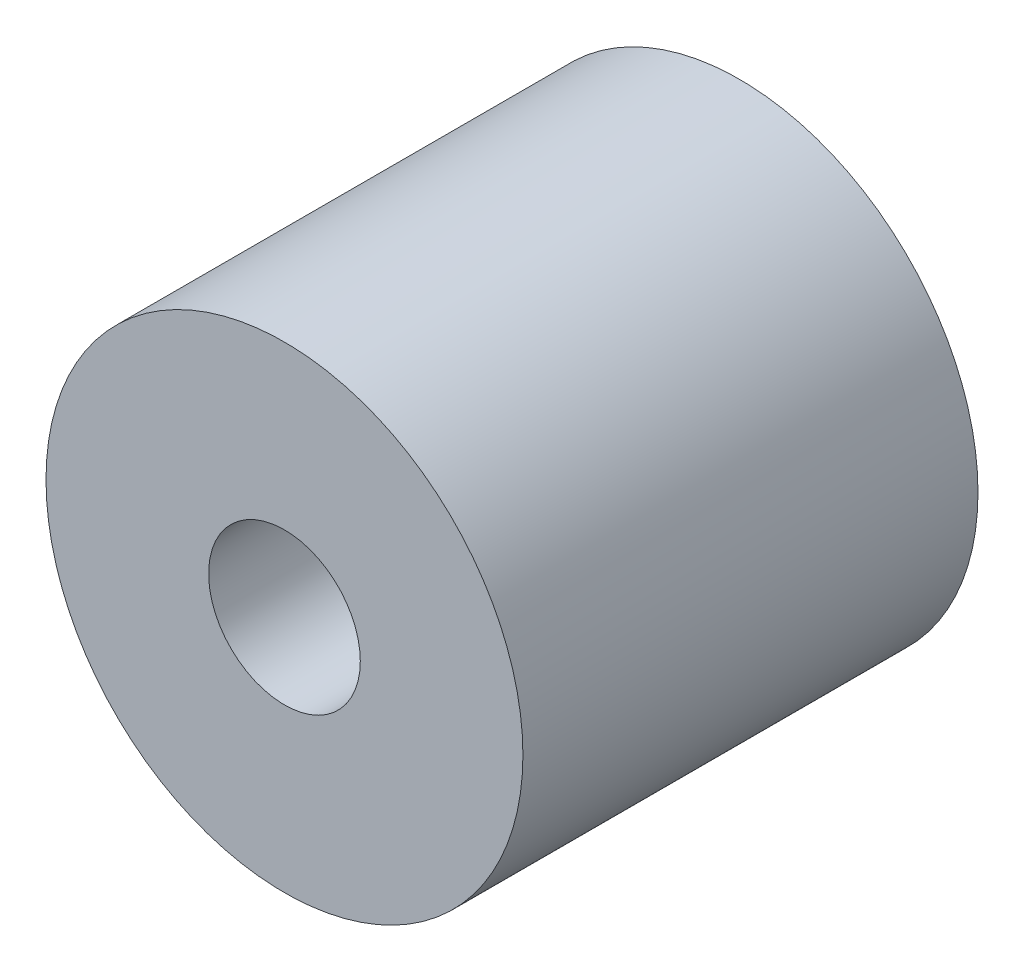
SolidWorks part; units mm, degrees
ref_plane "Front Plane" through (0, 0, 0) normal (0, 0, 1) x (1, 0, 0)
ref_plane "Top Plane" through (0, 0, 0) normal (0, 1, 0) x (1, 0, 0)
ref_plane "Right Plane" through (0, 0, 0) normal (1, 0, 0) x (0, 0, -1)
sketch "Sketch1" plane through (0, 0, 0) normal (0, 0, 1) x (1, 0, 0)
  circle A0 centre (0, 0) radius 1.5875
  circle A1 centre (0, 0) radius 4.9911
  dimension "D1" = 3.175
  dimension "D2" = 9.9822
extrude "Boss-Extrude1" add sketch "Sketch1" along normal blind 9.525
